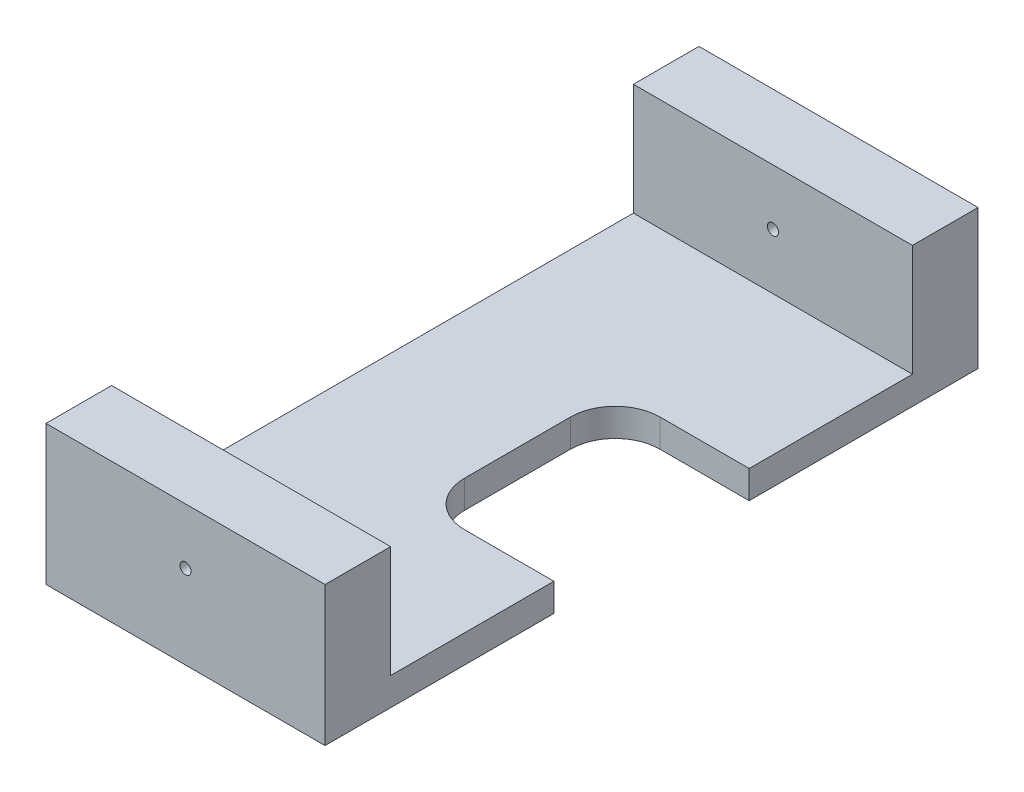
SolidWorks part; units mm, degrees
ref_plane "Alzado" through (0, 0, 0) normal (0, 0, 1) x (1, 0, 0)
ref_plane "Planta" through (0, 0, 0) normal (0, 1, 0) x (1, 0, 0)
ref_plane "Vista lateral" through (0, 0, 0) normal (1, 0, 0) x (0, 0, -1)
sketch "Croquis1" plane through (0, 0, 0) normal (0, 1, 0) x (1, 0, 0)
  line L1 (-25, -58.5) -> (25, -58.5)
  line L2 (-25, -58.5) -> (-25, 58.5)
  line L3 (-25, 58.5) -> (25, 58.5)
  line L4 (25, -58.5) -> (25, 58.5)
  line L5 (-25, -58.5) -> (25, 58.5) construction
  line L6 (-25, 58.5) -> (25, -58.5) construction
  point P0 (0, 0)
  dimension "D1" = 117
  dimension "D2" = 50
extrude "Saliente-Extruir1" add sketch "Croquis1" along normal blind 5 contours L3 L4 L1 L2
sketch "Croquis2" plane through (0, 5, 0) normal (0, 1, 0) x (1, 0, 0)
  line L0 (-25, 58.5) -> (-25, 46.75)
  line L1 (-25, -58.5) -> (-25, 58.5) construction
  line L2 (-25, 46.75) -> (25, 46.75)
  line L3 (25, -58.5) -> (25, 58.5) construction
  line L4 (25, 46.75) -> (25, 58.5)
  line L5 (25, 58.5) -> (-25, 58.5)
  line L6 (-25, -58.5) -> (-25, -46.75)
  line L7 (-25, -46.75) -> (25, -46.75)
  line L8 (25, -46.75) -> (25, -58.5)
  line L9 (25, -58.5) -> (-25, -58.5)
  dimension "D1" = 11.75
extrude "Saliente-Extruir2" add sketch "Croquis2" along normal blind 20
sketch "Croquis3" plane through (0, 5, 0) normal (0, 1, 0) x (1, 0, 0)
  line L0 (25, 17.5) -> (9, 17.5)
  line L1 (25, -46.75) -> (25, 46.75) construction
  line L2 (1, 9.5) -> (1, -9.5)
  line L3 (9, -17.5) -> (25, -17.5)
  line L4 (25, -17.5) -> (25, 17.5)
  line L5 (-13.75, 0) -> (13.75, 0) construction
  arc A0 (1, -9.5) -> (9, -17.5) centre (9, -9.5) ccw
  arc A1 (9, 17.5) -> (1, 9.5) centre (9, 9.5) ccw
  point P12 (1, 17.5)
  dimension "D4" = 8
  dimension "D1" = 35
  dimension "D2" = 17.5
  dimension "D3" = 24
extrude "Cortar-Extruir1" cut sketch "Croquis3" against normal blind 10
sketch "Croquis5" plane through (0, 0, -58.5) normal (0, 0, -1) x (-1, 0, 0)
  line L0 (0, 13.75) -> (0, -13.75) construction
  line L1 (-25, 25) -> (25, 25)
  line L2 (-25, 25) -> (-25, 5)
  line L3 (-25, 5) -> (25, 5)
  line L4 (25, 25) -> (25, 5)
  circle A0 centre (0, 15) radius 1
  dimension "D2" = 2
  dimension "D1" = 10
extrude "Cortar-Extruir3" cut sketch "Croquis5" against normal through all contours A0
